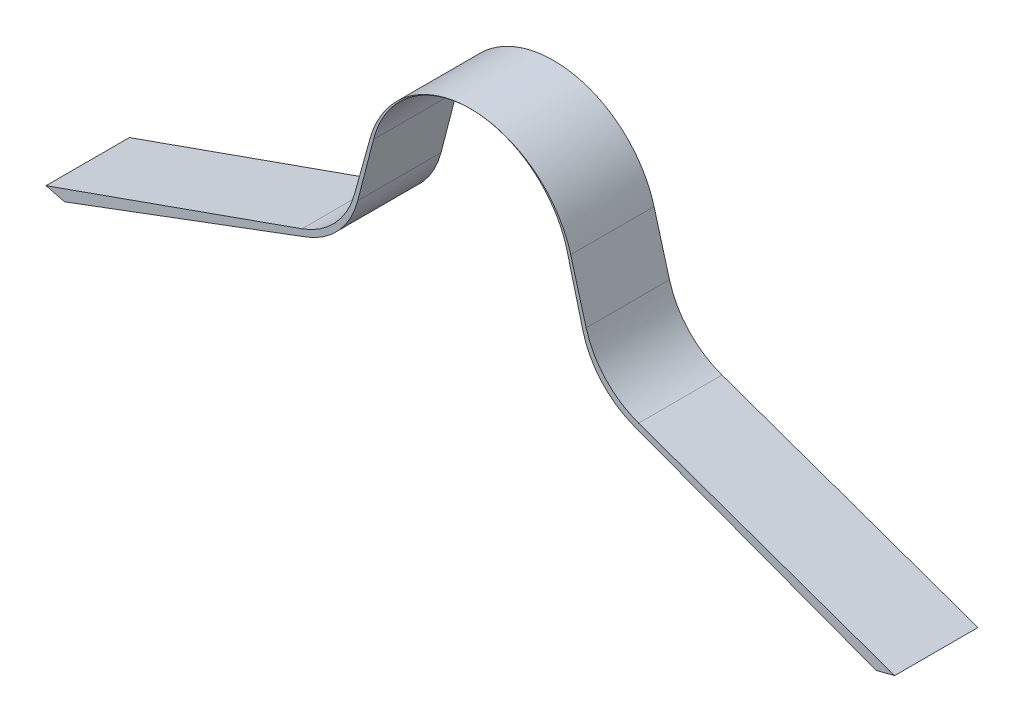
SolidWorks part; units mm, degrees
ref_plane "Спереди" through (0, 0, 0) normal (0, 0, 1) x (1, 0, 0)
ref_plane "Сверху" through (0, 0, 0) normal (0, 1, 0) x (1, 0, 0)
ref_plane "Справа" through (0, 0, 0) normal (1, 0, 0) x (0, 0, -1)
sketch "Эскиз1" plane through (0, 0, 0) normal (0, 0, 1) x (1, 0, 0)
  line L0 (0, 2.7717) -> (0, -0.6801) construction
  line L1 (-4.8684, -1.123) -> (-1.969, -0.0389)
  line L2 (-1.3511, 0.6473) -> (-1.1618, 1.3793)
  line L3 (4.8684, -1.123) -> (1.969, -0.0389)
  line L4 (1.3511, 0.6473) -> (1.1618, 1.3793)
  line L5 (0, 1.1402) -> (0, -2.3116) construction
  line L6 (-5.0913, -1.0664) -> (-2.0194, 0.0214)
  line L7 (-1.3895, 0.6968) -> (-1.2045, 1.3639)
  line L8 (5.0913, -1.0664) -> (2.0194, 0.0214)
  line L9 (1.3895, 0.6968) -> (1.2045, 1.3639)
  line L10 (-5.0913, -1.0664) -> (-4.8684, -1.123)
  line L11 (5.0913, -1.0664) -> (4.8684, -1.123)
  arc A0 (-1.1618, 1.3793) -> (1.1618, 1.3793) centre (0, 1.0788) cw
  arc A1 (-1.3511, 0.6473) -> (-1.969, -0.0389) centre (-2.3192, 0.8977) cw
  arc A2 (1.3511, 0.6473) -> (1.969, -0.0389) centre (2.3192, 0.8977) ccw
  arc A3 (-1.2045, 1.3639) -> (1.2045, 1.3639) centre (0, 1.0298) cw
  arc A4 (-1.3895, 0.6968) -> (-2.0194, 0.0214) centre (-2.3532, 0.964) cw
  arc A5 (1.3895, 0.6968) -> (2.0194, 0.0214) centre (2.3532, 0.964) ccw
  point P7 (0, 2.2788)
  point P8 (0, 2.2798)
  point P17 (-3.125, -0.4712)
  point P24 (0, 2.2798)
  point P32 (-3.125, -0.3702)
  dimension "D1" = 1.2
  dimension "D4" = 1
  dimension "D7" = 1.25
  dimension "D13" = 1
  dimension "D2" = 14.5
  dimension "D3" = 69.5
  dimension "D5" = 6.25
  dimension "D6" = 2.75
  dimension "D8" = 15.5
  dimension "D9" = 70.5
  dimension "D10" = 2.65
  dimension "D11" = 6.25
  dimension "D12" = 0.001
extrude "Бобышка-Вытянуть1" add sketch "Эскиз1" along normal blind 1
